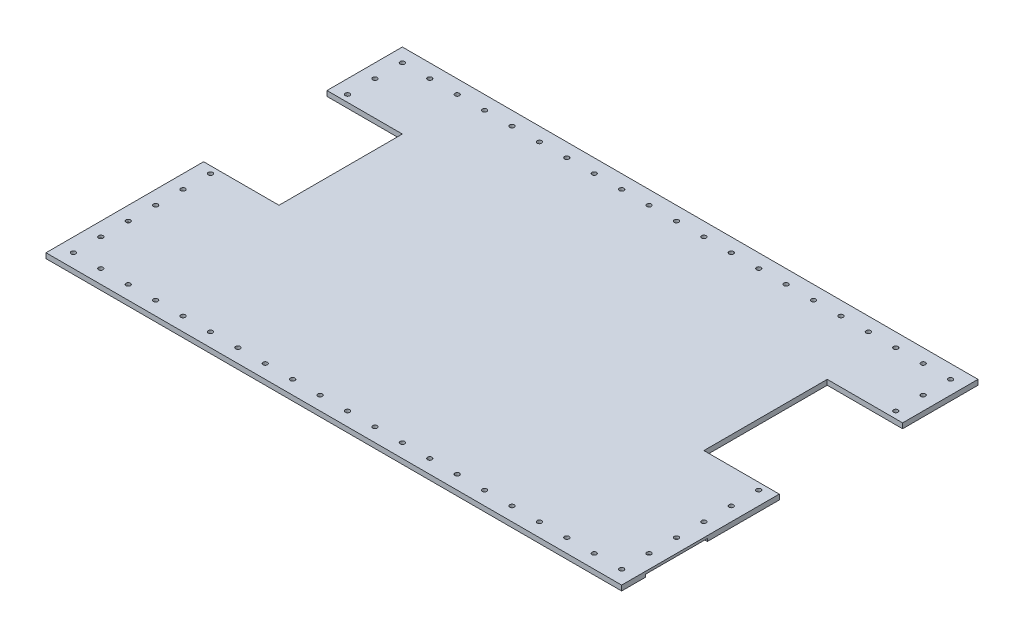
SolidWorks part; units mm, degrees
ref_plane "Front Plane" through (0, 0, 0) normal (0, 0, 1) x (1, 0, 0)
ref_plane "Top Plane" through (0, 0, 0) normal (0, 1, 0) x (1, 0, 0)
ref_plane "Right Plane" through (0, 0, 0) normal (1, 0, 0) x (0, 0, -1)
sketch "Sketch1" plane through (0, 0, 0) normal (0, 1, 0) x (1, 0, 0)
  line L1 (-266.7, -165.1) -> (266.7, -165.1)
  line L2 (-266.7, -165.1) -> (-266.7, 165.1)
  line L3 (-266.7, 165.1) -> (266.7, 165.1)
  line L4 (266.7, -165.1) -> (266.7, 165.1)
  line L5 (-266.7, -165.1) -> (266.7, 165.1) construction
  line L6 (-266.7, 165.1) -> (266.7, -165.1) construction
  point P0 (0, 0)
  dimension "D1" = 330.2
  dimension "D2" = 533.4
extrude "Boss-Extrude1" add sketch "Sketch1" along normal blind 4.7625
sketch "Sketch2" plane through (0, 4.7625, 0) normal (0, 1, 0) x (1, 0, 0)
  line L0 (-266.7, -165.1) -> (266.7, -165.1) construction
  line L1 (-266.7, 165.1) -> (-266.7, -165.1) construction
  circle A0 centre (-254, -152.4) radius 2.0701
  dimension "D1" = 4.1402
  dimension "D2" = 12.7
  dimension "D3" = 12.7
extrude "Cut-Extrude1" cut sketch "Sketch2" against normal through all
pattern_linear "LPattern1" count 23 spacing 25.4 along (1, 0, 0) of "Cut-Extrude1"
pattern_linear "LPattern2" count 32 spacing 25.4 along (0, 0, -1) of "Cut-Extrude1"
mirror "Mirror2" about plane through (0, 0, 0) normal (1, 0, 0) of "LPattern2"
mirror "Mirror3" about plane through (0, 0, 0) normal (0, 0, 1) of "LPattern1"
sketch "Sketch3" plane through (0, 0, 0) normal (0, -1, 0) x (1, 0, 0)
  line L0 (-266.7, -165.1) -> (-266.7, 165.1) construction
  line L1 (-266.7, 142.875) -> (-241.3, 142.875)
  line L2 (-266.7, 142.875) -> (-266.7, 85.725)
  line L3 (-266.7, 85.725) -> (-241.3, 85.725)
  line L4 (-238.125, 139.7) -> (-238.125, 88.9)
  line L5 (-266.7, 165.1) -> (266.7, 165.1) construction
  line L6 (0, -165.1) -> (0, 165.1) construction
  line L7 (266.7, -165.1) -> (-266.7, -165.1) construction
  line L8 (266.7, 85.725) -> (241.3, 85.725)
  line L9 (238.125, 139.7) -> (238.125, 88.9)
  line L10 (266.7, 142.875) -> (241.3, 142.875)
  line L11 (266.7, 85.725) -> (266.7, 142.875)
  arc A0 (-238.125, 139.7) -> (-241.3, 142.875) centre (-241.3, 139.7) ccw
  arc A1 (-238.125, 88.9) -> (-241.3, 85.725) centre (-241.3, 88.9) cw
  arc A2 (238.125, 88.9) -> (241.3, 85.725) centre (241.3, 88.9) ccw
  arc A3 (238.125, 139.7) -> (241.3, 142.875) centre (241.3, 139.7) cw
  dimension "D4" = 3.175
  dimension "D1" = 22.225
  dimension "D2" = 28.575
  dimension "D3" = 57.15
extrude "Cut-Extrude2" cut sketch "Sketch3" against normal blind 2.3812
sketch "Sketch4" plane through (0, 4.7625, 0) normal (0, 1, 0) x (1, 0, 0)
  line L0 (0, 165.1) -> (0, -165.1) construction
  line L1 (266.7, 165.1) -> (-266.7, 165.1) construction
  line L2 (-266.7, -165.1) -> (266.7, -165.1) construction
  line L3 (266.7, -165.1) -> (266.7, 165.1) construction
  line L4 (266.7, 95.25) -> (196.85, 95.25)
  line L5 (266.7, 95.25) -> (266.7, -19.05)
  line L6 (266.7, -19.05) -> (196.85, -19.05)
  line L7 (196.85, 95.25) -> (196.85, -19.05)
  line L8 (-266.7, 95.25) -> (-266.7, -19.05)
  line L9 (-266.7, 95.25) -> (-196.85, 95.25)
  line L10 (-196.85, 95.25) -> (-196.85, -19.05)
  line L11 (-266.7, -19.05) -> (-196.85, -19.05)
  dimension "D1" = 184.15
  dimension "D2" = 69.85
  dimension "D3" = 69.85
extrude "Cut-Extrude3" cut sketch "Sketch4" against normal through all
